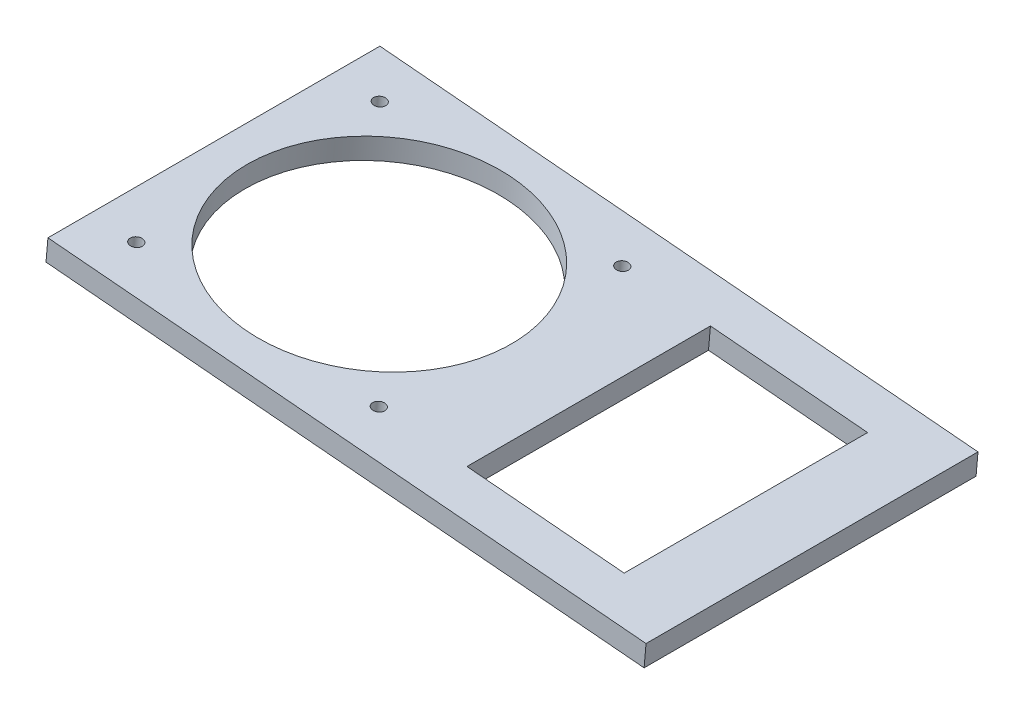
SolidWorks part; units mm, degrees
ref_plane "Front Plane" through (0, 0, 0) normal (0, 0, 1) x (1, 0, 0)
ref_plane "Top Plane" through (0, 0, 0) normal (0, 1, 0) x (1, 0, 0)
ref_plane "Right Plane" through (0, 0, 0) normal (1, 0, 0) x (0, 0, -1)
sketch "Sketch1" plane through (0, 0, 0) normal (0, 0, 1) x (1, 0, 0)
  line L0 (0, 0) -> (36.6665, 419.1) construction
  line L1 (36.6665, 419.1) -> (155.7226, 419.1) construction
  line L2 (155.7226, 419.1) -> (155.7226, 0) construction
  line L3 (155.7226, 0) -> (0, 0) construction
  line L4 (155.7226, -1000) -> (155.7226, 49000) construction
  line L5 (1.8042, 20.6221) -> (36.6665, 419.1) construction
  line L6 (1.8042, 20.6221) -> (41.652, 17.1359) construction
  line L7 (36.6665, 419.1) -> (76.5143, 415.6138) construction
  line L8 (41.652, 17.1359) -> (76.5143, 415.6138) construction
  line L9 (60.4726, -1000) -> (60.4726, 49000) construction
  line L10 (-52.7184, 317.5) -> (-128.6284, 324.1413) construction
  line L11 (-30.1965, 414.3375) -> (36.6601, 414.3375) construction
  line L12 (-1162.1335, 304.8) -> (48837.8665, 304.8) construction
  line L13 (-130.0274, 292.1) -> (-53.8274, 292.1) construction
  line L14 (-128.6284, 324.1413) -> (-53.8274, 292.1) construction
  line L15 (-52.7184, 317.5) -> (-130.0274, 292.1) construction
  line L16 (36.6601, 338.1375) -> (-30.1965, 338.1375) construction
  line L17 (-138.1172, 324.9714) -> (27.1662, 310.511)
  line L18 (-138.1172, 324.9714) -> (-137.5638, 331.2973)
  line L19 (-137.5638, 331.2973) -> (36.6665, 419.1)
  line L20 (36.6665, 419.1) -> (104.9226, 419.1)
  line L21 (104.9226, 419.1) -> (104.9226, 0) construction
  line L22 (27.1662, 310.511) -> (0.3389, 3.8741)
  line L23 (0.3389, 3.8741) -> (44.6198, 0)
  line L24 (44.6198, 0) -> (104.9226, 0)
  line L25 (104.9226, 419.1) -> (155.7226, 311.15)
  line L26 (155.7226, 311.15) -> (155.7226, 304.8)
  line L27 (155.7226, 304.8) -> (104.9226, 280.8941)
  line L28 (104.9226, 280.8941) -> (104.9226, 0)
  arc A0 (-128.6284, 324.1413) -> (-30.1965, 414.3375) centre (-30.1965, 315.5296) cw construction
  arc A1 (69.9976, 304.8) -> (36.6601, 338.1375) centre (36.6601, 304.8) ccw construction
  arc A2 (146.1976, 304.8) -> (36.6601, 414.3375) centre (36.6601, 304.8) ccw construction
  arc A3 (-52.7184, 317.5) -> (-30.1965, 338.1375) centre (-30.1965, 315.5296) cw construction
  point P7 (54.1226, 400.05)
  point P17 (146.1976, 304.8)
  point P18 (69.9976, 304.8)
  dimension "D9" = 9.525
  dimension "D14" = 25.4
  dimension "D1" = 419.1
  dimension "D2" = 101.6
  dimension "D3" = 19.05
  dimension "D4" = 19.05
  dimension "D5" = 85
  dimension "D6" = 40
  dimension "D7" = 400
  dimension "D8" = 95.25
  dimension "D10" = 9.525
  dimension "D11" = 114.3
  dimension "D12" = 76.2
  dimension "D13" = 9.525
  dimension "D15" = 127
  dimension "D16" = 9.525
  dimension "D17" = 209.55
  dimension "D18" = 6.35
  dimension "D19" = 50.8
  dimension "D20" = 44.45
  dimension "D21" = 6.35
sketch "Sketch2" plane through (0, 0, 0) normal (0, 0, 1) x (1, 0, 0)
  line L0 (-137.5638, 331.2973) -> (-138.1172, 324.9714)
  line L1 (-137.5638, 331.2973) -> (34.0455, 316.2834)
  line L2 (-138.1172, 324.9714) -> (33.492, 309.9576)
  line L3 (34.0455, 316.2834) -> (33.492, 309.9576)
  line L8 (27.1662, 310.511) -> (0.3389, 3.8741) construction
  dimension "D1" = 6.35
extrude "Boss-Extrude1" add sketch "Sketch2" along normal blind 95.25
sketch "Sketch3" plane through (27.7196, 316.8368, 0) normal (0.0872, 0.9962, 0) x (0.9962, -0.0872, 0)
  line L0 (-118.2897, -47.625) -> (-118.2897, 0) construction
  line L1 (-156.3897, 0) -> (-80.1897, 0) construction
  line L2 (-165.9147, -47.625) -> (-118.2897, -47.625) construction
  line L3 (-165.9147, -95.25) -> (-165.9147, 0) construction
  circle A0 centre (-118.2897, -47.625) radius 38.1
  dimension "D1" = 76.2
extrude "Cut-Extrude1" cut sketch "Sketch3" against normal through all
sketch "Sketch4" plane through (27.7196, 316.8368, 0) normal (0.0872, 0.9962, 0) x (0.9962, -0.0872, 0)
  line L1 (-83.3647, -82.55) -> (-153.2147, -82.55) construction
  line L2 (-83.3647, -82.55) -> (-83.3647, -12.7) construction
  line L3 (-83.3647, -12.7) -> (-153.2147, -12.7) construction
  line L4 (-153.2147, -82.55) -> (-153.2147, -12.7) construction
  line L5 (-83.3647, -82.55) -> (-153.2147, -12.7) construction
  line L6 (-83.3647, -12.7) -> (-153.2147, -82.55) construction
  circle A0 centre (-153.2147, -12.7) radius 1.75
  circle A1 centre (-153.2147, -82.55) radius 1.75
  circle A2 centre (-83.3647, -82.55) radius 1.75
  circle A3 centre (-83.3647, -12.7) radius 1.75
  point P0 (-118.2897, -47.625)
  dimension "D2" = 3.5
  dimension "D1" = 69.85
extrude "Cut-Extrude2" cut sketch "Sketch4" against normal through all
sketch "Sketch5" plane through (27.7196, 316.8368, 0) normal (0.0872, 0.9962, 0) x (0.9962, -0.0872, 0)
  line L0 (-165.9147, -95.25) -> (-165.9147, 0) construction
  line L1 (-57.9647, -12.7) -> (-12.7, -12.7)
  line L2 (-57.9647, -12.7) -> (-57.9647, -82.55)
  line L3 (-57.9647, -82.55) -> (-12.7, -82.55)
  line L4 (-12.7, -12.7) -> (-12.7, -82.55)
  line L5 (6.35, -95.25) -> (-165.9147, -95.25) construction
  line L6 (-154.9908, 0) -> (-79.0808, 0) construction
  point P10 (0, 0)
  dimension "D1" = 107.95
  dimension "D2" = 12.7
  dimension "D3" = 12.7
  dimension "D4" = 12.7
extrude "Cut-Extrude3" cut sketch "Sketch5" against normal through all
